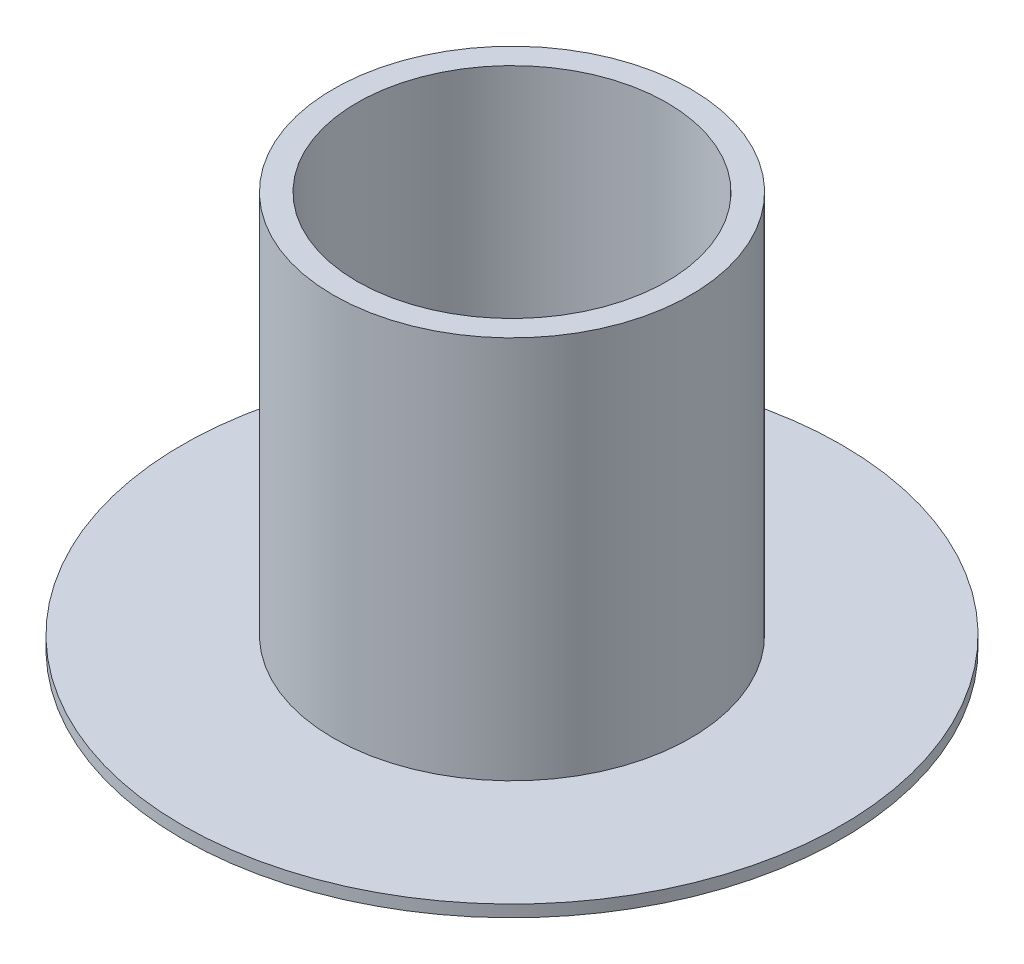
SolidWorks part; units mm, degrees
ref_plane "Alzado" through (0, 0, 0) normal (0, 0, 1) x (1, 0, 0)
ref_plane "Planta" through (0, 0, 0) normal (0, 1, 0) x (1, 0, 0)
ref_plane "Vista lateral" through (0, 0, 0) normal (1, 0, 0) x (0, 0, -1)
sketch "Croquis1" plane through (0, 0, 0) normal (0, 0, 1) x (1, 0, 0)
  line L0 (-49.7706, 52.5116) -> (-49.7706, -30.1296) construction
  line L1 (-49.7706, -30.1296) -> (-49.7706, 11.191) construction
  line L2 (-49.7706, 11.191) -> (-61.5206, 11.191) construction
  line L3 (-61.5206, 11.191) -> (-74.7706, 11.191)
  line L4 (-74.7706, 11.191) -> (-74.7706, 12.091)
  line L5 (-74.7706, 12.091) -> (-63.3206, 12.091)
  line L6 (-63.3206, 12.091) -> (-63.3206, 41.191)
  line L7 (-63.3206, 41.191) -> (-61.5206, 41.191)
  line L8 (-61.5206, 41.191) -> (-61.5206, 11.191)
  dimension "D1" = 11.75
  dimension "D2" = 13.25
  dimension "D3" = 11.45
revolve "Revolución1" add sketch "Croquis1" angle 360 about L0
